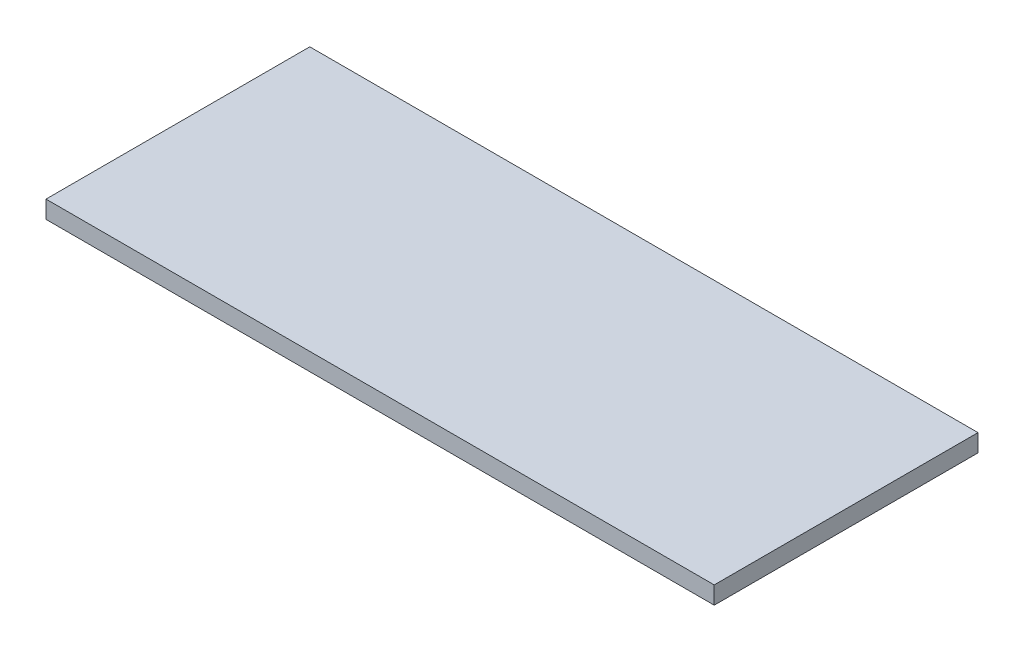
SolidWorks part; units mm, degrees
ref_plane "Front Plane" through (0, 0, 0) normal (0, 0, 1) x (1, 0, 0)
ref_plane "Top Plane" through (0, 0, 0) normal (0, 1, 0) x (1, 0, 0)
ref_plane "Right Plane" through (0, 0, 0) normal (1, 0, 0) x (0, 0, -1)
sketch "Sketch1" plane through (0, 0, 0) normal (0, 1, 0) x (1, 0, 0)
  line L1 (0, 0) -> (304, 0)
  line L2 (0, 0) -> (0, 120)
  line L3 (0, 120) -> (304, 120)
  line L4 (304, 0) -> (304, 120)
  dimension "D1" = 120
  dimension "D2" = 304
extrude "Boss-Extrude1" add sketch "Sketch1" along normal blind 8
